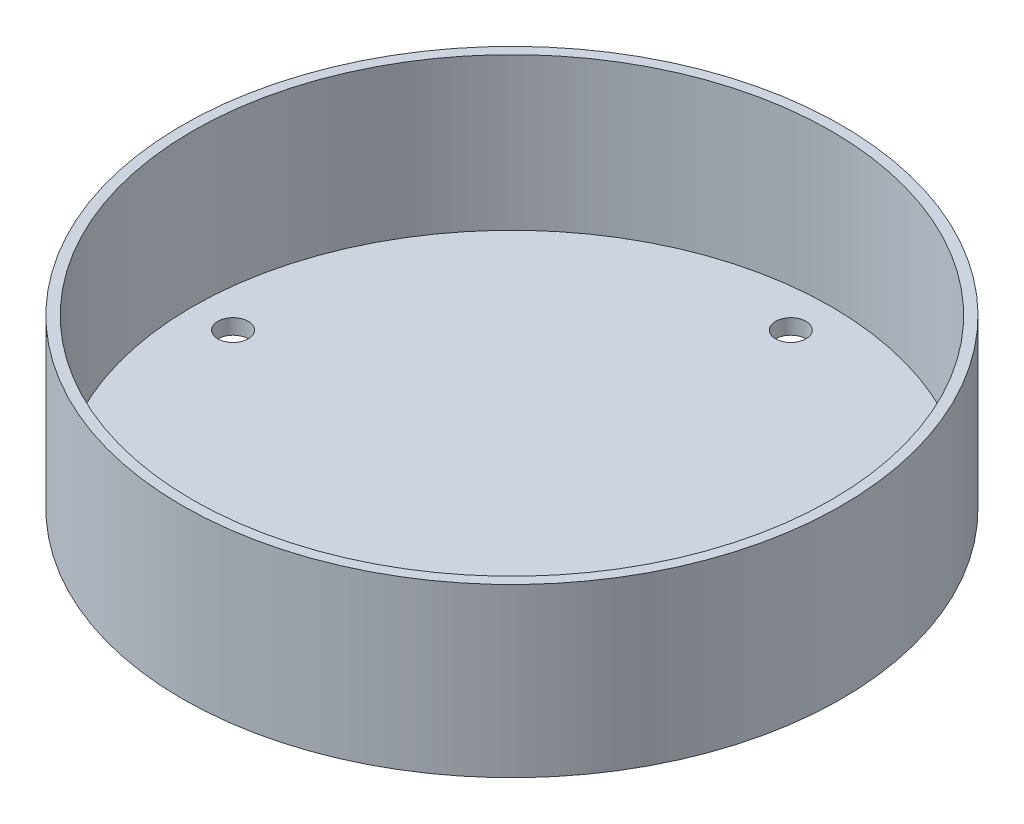
SolidWorks part; units mm, degrees
ref_plane "Front Plane" through (0, 0, 0) normal (0, 0, 1) x (1, 0, 0)
ref_plane "Top Plane" through (0, 0, 0) normal (0, 1, 0) x (1, 0, 0)
ref_plane "Right Plane" through (0, 0, 0) normal (1, 0, 0) x (0, 0, -1)
sketch "Sketch1" plane through (0, 0, 0) normal (0, 1, 0) x (1, 0, 0)
  circle A0 centre (0, 0) radius 65
  dimension "160" = 130
extrude "Boss-Extrude1" add sketch "Sketch1" along normal blind 3
sketch "Sketch2" plane through (0, 3, 0) normal (0, 1, 0) x (1, 0, 0)
  circle A0 centre (0, 0) radius 55 construction
  circle A1 centre (0, 55) radius 3
  dimension "D1" = 110
  dimension "D2" = 6
extrude "Cut-Extrude1" cut sketch "Sketch2" against normal through all
pattern_circular "CirPattern1" count 4 over 360 about axis through (0, 0, 0) along (0, 1, 0) of "Cut-Extrude1"
sketch "Sketch3" plane through (0, 3, 0) normal (0, 1, 0) x (1, 0, 0)
  circle A0 centre (0, 0) radius 65
  circle A1 centre (0, 0) radius 63
  dimension "D1" = 130
  dimension "D2" = 126
extrude "Boss-Extrude2" add sketch "Sketch3" along normal blind 30
